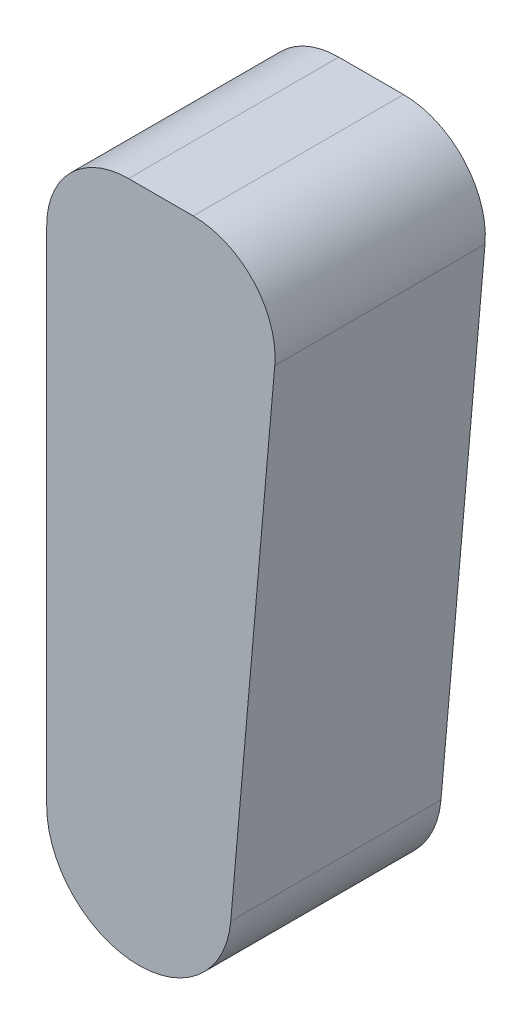
SolidWorks part; units mm, degrees
ref_plane "Plan de face" through (0, 0, 0) normal (0, 0, 1) x (1, 0, 0)
ref_plane "Plan de dessus" through (0, 0, 0) normal (0, 1, 0) x (1, 0, 0)
ref_plane "Plan de droite" through (0, 0, 0) normal (1, 0, 0) x (0, 0, -1)
sketch "Esquisse2" plane through (0, 0, 0) normal (0, 0, 1) x (1, 0, 0)
  line L0 (-7.8913, 50) -> (12.2959, 50)
  line L2 (-7.8913, 25) -> (10.1087, 25) construction
  line L3 (-7.8913, 50) -> (-7.8913, 0)
  line L6 (12.2959, 50) -> (7.8613, -0.6878)
  arc A0 (7.8613, -0.6878) -> (-7.8913, 0) centre (0, 0) cw
  dimension "D2" = 18
  dimension "D1" = 50
  dimension "D3" = 85
extrude "Boss.-Extru.1" add sketch "Esquisse2" along normal blind 18
fillet "Congé1" radius 7 2 edges at (12.2959, 50, 9) (-7.8913, 50, 9)
sketch "Esquisse3" plane through (0, 0, 0) normal (0, 0, -1) x (-1, 0, 0)
  line L0 (-11.6567, 43) -> (7.8913, 43) construction
  arc A0 (-4.6567, 50) -> (-11.6301, 42.3899) centre (-4.6567, 43) ccw construction
  dimension "D1" = 19.5481
equation "\"D1@Boss.-Extru.2\" = \"thickness\""
equation "\"D7@Esquisse1\" = \"tool_diameter\" / 2"
equation "\"D6@Esquisse1\" = \"thickness\" / 2"
equation "\"D5@Esquisse1\" = \"thickness\" / 2"
equation "\"D1@Boss.-Extru.1\" = \"material_thickness\""
equation "\"D2@Esquisse2\"= \"material_thickness\""
equation "\"D1@Congé1\"=\"fillet\""
equation "\"tool_diameter\"=9"
equation "\"hole_clearance\"=0.5"
equation "\"material_thickness\"=18"
equation "\"clearance\"=0.5"
equation "\"outer_slot\"=0.5"
equation "\"fillet\"=7"
